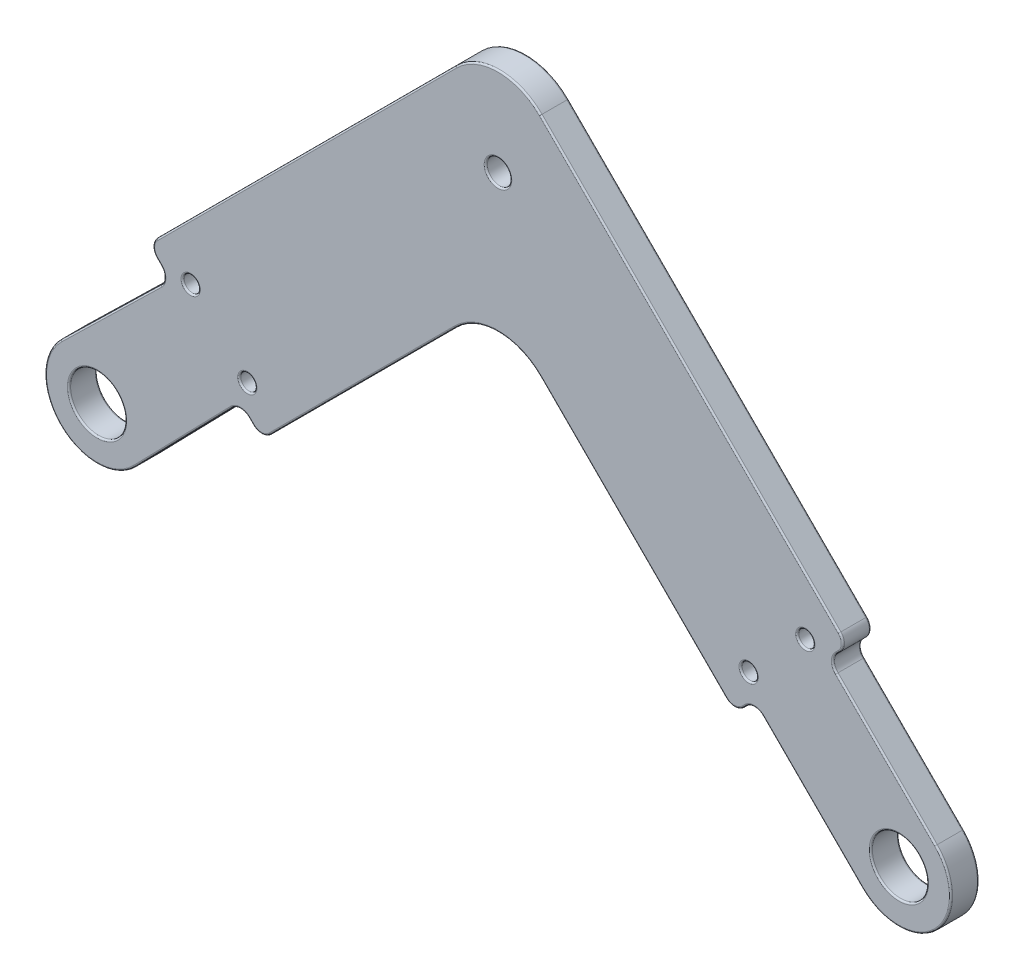
SolidWorks part; units mm, degrees
ref_plane "Front Plane" through (0, 0, 0) normal (0, 0, 1) x (1, 0, 0)
ref_plane "Top Plane" through (0, 0, 0) normal (0, 1, 0) x (1, 0, 0)
ref_plane "Right Plane" through (0, 0, 0) normal (1, 0, 0) x (0, 0, -1)
sketch "Sketch1" plane through (0, 0, 0) normal (0, 0, 1) x (1, 0, 0)
  line L0 (-100, 0) -> (100, 0) construction
  line L1 (-100, 0) -> (0, 100) construction
  line L2 (0, 100) -> (100, 0) construction
  line L3 (0, 0) -> (-50, 50) construction
  line L4 (-40, 60) -> (40, 60) construction
  line L5 (0, 100) -> (0, 60) construction
  line L6 (-56.5165, 43.4835) -> (-40, 60)
  line L7 (-40, 60) -> (40, 60)
  line L8 (40, 60) -> (86.565, 13.435) construction
  line L9 (-49.4454, 36.4124) -> (-35.8579, 50)
  line L10 (-35.8579, 50) -> (35.8579, 50)
  line L11 (35.8579, 50) -> (79.4939, 6.364)
  line L12 (-63.5876, 50.5546) -> (-44.1421, 70)
  line L13 (-44.1421, 70) -> (44.1421, 70)
  line L14 (44.1421, 70) -> (93.636, 20.5061)
  line L15 (-63.5876, 50.5546) -> (-49.4454, 36.4124)
  line L16 (93.636, 20.5061) -> (79.4939, 6.364)
  line L17 (91.1612, 18.0312) -> (104.5962, 4.5962)
  line L18 (81.9688, 8.8388) -> (95.4038, -4.5962)
  line L19 (90.1005, 24.0416) -> (75.9584, 9.8995) construction
  line L20 (6, 70) -> (3.4304, 82.6944)
  line L21 (-6, 70) -> (-3.4304, 82.6944)
  line L22 (40, 60) -> (86.565, 13.435)
  circle A0 centre (-100, 0) radius 20
  circle A1 centre (0, 0) radius 20
  circle A2 centre (100, 0) radius 20
  circle A3 centre (100, 0) radius 10 construction
  circle A4 centre (100, 0) radius 3.5
  arc A5 (95.4038, -4.5962) -> (104.5962, 4.5962) centre (100, 0) ccw
  circle A6 centre (100, 0) radius 6.5 construction
  circle A7 centre (79.4939, 13.435) radius 1
  circle A8 centre (86.565, 20.5061) radius 1
  circle A9 centre (0, 60) radius 1.5
  circle A10 centre (0, 82) radius 1.5
  arc A11 (3.4304, 82.6944) -> (-3.4304, 82.6944) centre (0, 82) ccw
  circle A12 centre (0, 82) radius 3.5 construction
  circle A13 centre (-50, 50) radius 1.5
  point P2 (0, 0)
  dimension "D5" = 40
  dimension "D9" = 20
  dimension "D10" = 7
  dimension "D14" = 2
  dimension "D17" = 3
  dimension "D22" = 3
  dimension "D1" = 200
  dimension "D2" = 90
  dimension "D3" = 90
  dimension "D4" = 80
  dimension "D8" = 27.5
  dimension "D12" = 19
  dimension "D13" = 5
  dimension "D15" = 5
  dimension "D16" = 5
  dimension "D18" = 12
  dimension "D20" = 6
  dimension "D21" = 6
  dimension "D6" = 10
  dimension "D7" = 10
  dimension "D11" = 3
  dimension "D19" = 2
sketch "Sketch2" plane through (0, 0, 0) normal (0, 0, 1) x (1, 0, 0)
  line L0 (-86.565, 13.435) -> (-50, 50) construction
  line L1 (-100, 0) -> (0, 100) construction
  line L2 (-50, 50) -> (-13.435, 13.435) construction
  line L3 (0, 0) -> (-50, 50) construction
  line L4 (-79.4939, 6.364) -> (-50, 35.8579)
  line L5 (-50, 35.8579) -> (-20.5061, 6.364)
  line L6 (-93.636, 20.5061) -> (-50, 64.1421)
  line L7 (-50, 64.1421) -> (-6.364, 20.5061)
  line L8 (-93.636, 20.5061) -> (-50, 64.1421) construction
  line L9 (-79.4939, 6.364) -> (-50, 35.8579) construction
  line L10 (-93.636, 20.5061) -> (-79.4939, 6.364)
  line L11 (-6.364, 20.5061) -> (-20.5061, 6.364)
  line L12 (-104.534, 4.6576) -> (-90.9809, 17.8509)
  line L13 (-95.3424, -4.534) -> (-82.1491, 9.0191)
  line L14 (-18.0312, 8.8388) -> (-4.5962, -4.5962)
  line L15 (-8.8388, 18.0312) -> (4.5962, 4.5962)
  line L16 (-91.8683, 22.2739) -> (-77.7261, 8.1317) construction
  line L17 (-8.1317, 22.2739) -> (-22.2739, 8.1317) construction
  circle A0 centre (-100, 0) radius 3.5
  circle A1 centre (-100, 0) radius 10 construction
  circle A2 centre (0, 0) radius 3.5
  circle A3 centre (0, 0) radius 10 construction
  arc A4 (-4.5962, -4.5962) -> (4.5962, 4.5962) centre (0, 0) ccw
  arc A5 (-104.534, 4.6576) -> (-95.3424, -4.534) centre (-100, 0) ccw
  circle A6 centre (-100, 0) radius 20 construction
  circle A7 centre (-100, 0) radius 6.5 construction
  circle A8 centre (0, 0) radius 6.5 construction
  circle A9 centre (-88.3327, 18.7383) radius 1
  circle A10 centre (-81.2617, 11.6673) radius 1
  circle A11 centre (-18.7383, 11.6673) radius 1
  circle A12 centre (-11.6673, 18.7383) radius 1
  dimension "D1" = 20
  dimension "D2" = 7
  dimension "D8" = 2
  dimension "D6" = 19
  dimension "D7" = 19
  dimension "D9" = 5
  dimension "D10" = 5
  dimension "D11" = 5
  dimension "D12" = 5
  dimension "D13" = 5
  dimension "D14" = 5
  dimension "D3" = 3
  dimension "D4" = 10
  dimension "D5" = 10
sketch "Sketch3" plane through (0, 0, 0) normal (0, 0, 1) x (1, 0, 0)
  line L0 (-95.3424, -4.534) -> (-82.1491, 9.0191) construction
  line L1 (-104.534, 4.6576) -> (-90.9809, 17.8509) construction
  line L2 (-18.0312, 8.8388) -> (-4.5962, -4.5962) construction
  line L3 (-8.8388, 18.0312) -> (4.5962, 4.5962) construction
  line L4 (-95.3424, -4.534) -> (-82.1491, 9.0191)
  line L5 (-104.534, 4.6576) -> (-90.9809, 17.8509)
  line L6 (-79.4939, 6.364) -> (-50, 35.8579)
  line L7 (-50, 35.8579) -> (-20.5061, 6.364)
  line L8 (-20.5061, 6.364) -> (-6.364, 20.5061)
  line L9 (-6.364, 20.5061) -> (-50, 64.1421)
  line L10 (-50, 64.1421) -> (-93.636, 20.5061)
  line L11 (-93.636, 20.5061) -> (-79.4939, 6.364)
  line L12 (-79.4939, 6.364) -> (-50, 35.8579)
  line L13 (-50, 35.8579) -> (-20.5061, 6.364)
  line L14 (-20.5061, 6.364) -> (-18.0312, 8.8388)
  line L15 (-6.364, 20.5061) -> (-50, 64.1421)
  line L16 (-50, 64.1421) -> (-93.636, 20.5061)
  line L17 (-93.636, 20.5061) -> (-90.9809, 17.8509)
  line L18 (-18.0312, 8.8388) -> (-4.5962, -4.5962)
  line L19 (-8.8388, 18.0312) -> (4.5962, 4.5962)
  line L20 (-82.1491, 9.0191) -> (-79.4939, 6.364)
  line L21 (-8.8388, 18.0312) -> (-6.364, 20.5061)
  arc A0 (-104.534, 4.6576) -> (-95.3424, -4.534) centre (-100, 0) ccw construction
  circle A1 centre (0, 0) radius 3.5
  circle A2 centre (0, 0) radius 3.5
  circle A3 centre (-100, 0) radius 3.5
  circle A4 centre (-100, 0) radius 3.5
  circle A5 centre (-18.7383, 11.6673) radius 1
  circle A6 centre (-18.7383, 11.6673) radius 1
  circle A7 centre (-81.2617, 11.6673) radius 1
  circle A8 centre (-81.2617, 11.6673) radius 1
  circle A9 centre (-88.3327, 18.7383) radius 1
  circle A10 centre (-88.3327, 18.7383) radius 1
  circle A11 centre (-11.6673, 18.7383) radius 1
  circle A12 centre (-11.6673, 18.7383) radius 1
  arc A13 (-4.5962, -4.5962) -> (4.5962, 4.5962) centre (0, 0) ccw construction
  arc A14 (-104.534, 4.6576) -> (-95.3424, -4.534) centre (-100, 0) ccw
  arc A15 (-4.5962, -4.5962) -> (4.5962, 4.5962) centre (0, 0) ccw
  dimension "D1" = 0
  dimension "D2" = 0
  dimension "D3" = 0
  dimension "D4" = 0
  dimension "D5" = 0
  dimension "D6" = 0
  dimension "D7" = 0
extrude "Boss-Extrude1" add sketch "Sketch3" along normal blind 3.5
fillet "Fillet3" radius 1.5 8 edges at (-82.1491, 9.0191, 1.75) (-79.4939, 6.364, 1.75) (-90.9809, 17.8509, 1.75) (-93.636, 20.5061, 1.75) (-20.5061, 6.364, 1.75) (-18.0312, 8.8388, 1.75) (-8.8388, 18.0312, 1.75) (-6.364, 20.5061, 1.75)
fillet "Fillet4" radius 7.5 2 edges at (-50, 35.8579, 1.75) (-50, 64.1421, 1.75)
sketch "Sketch4" plane through (0, 0, 3.5) normal (0, 0, 1) x (1, 0, 0)
  circle A0 centre (-50, 50) radius 1.524
  point P2 (-50, 50)
  dimension "D1" = 3.048
extrude "Cut-Extrude1" cut sketch "Sketch4" against normal blind 3.5
fillet "Fillet5" radius 0.2 62 edges at (-48.476, 50, 3.5) (-48.476, 50, 0) (-10.6673, 18.7383, 0) (-10.6673, 18.7383, 3.5) (-87.3327, 18.7383, 0) (-87.3327, 18.7383, 3.5) (-80.2617, 11.6673, 0) (-80.2617, 11.6673, 3.5) (-17.7383, 11.6673, 0) (-17.7383, 11.6673, 3.5) (-96.5, 0, 0) (-96.5, 0, 3.5) (3.5, 0, 0) (3.5, 0, 3.5) (-80.8143, 7.6844, 0) (-66.8683, 18.9896, 0) (-33.1317, 18.9896, 0) (-19.2687, 7.6014, 0) (-10.7834, 1.591, 0) (4.5962, -4.5962, 0) (-1.591, 10.7834, 0) (-7.6014, 19.2687, 0) (-26.0607, 40.2028, 0) (-73.9393, 40.2028, 0) (-92.3156, 19.1857, 0) (-98.3021, 10.724, 0) (-104.5962, -4.5962, 0) (-89.276, 1.6979, 0) (-80.8143, 7.6844, 3.5) (-66.8683, 18.9896, 3.5) (-33.1317, 18.9896, 3.5) (-19.2687, 7.6014, 3.5) (-10.7834, 1.591, 3.5) (4.5962, -4.5962, 3.5) (-1.591, 10.7834, 3.5) (-7.6014, 19.2687, 3.5) (-73.9393, 40.2028, 3.5) (-92.3156, 19.1857, 3.5) (-98.3021, 10.724, 3.5) (-104.5962, -4.5962, 3.5) (-89.276, 1.6979, 3.5) (-6.9853, 20.5061, 0) (-20.5061, 6.9853, 0) (-93.0147, 20.5061, 0) (-79.4939, 6.9853, 0) (-6.9853, 20.5061, 3.5) (-20.5061, 6.9853, 3.5) (-93.0147, 20.5061, 3.5) (-79.4939, 6.9853, 3.5) (-82.1448, 8.3834, 0) (-82.1448, 8.3834, 3.5) (-91.6166, 17.8552, 0) (-91.6166, 17.8552, 3.5) (-18.0312, 8.2175, 0) (-18.0312, 8.2175, 3.5) (-8.2175, 18.0312, 0) (-8.2175, 18.0312, 3.5) (-50, 61.0355, 0) (-50, 61.0355, 3.5) (-50, 32.7513, 0) (-50, 32.7513, 3.5) (-26.0607, 40.2028, 3.5)
